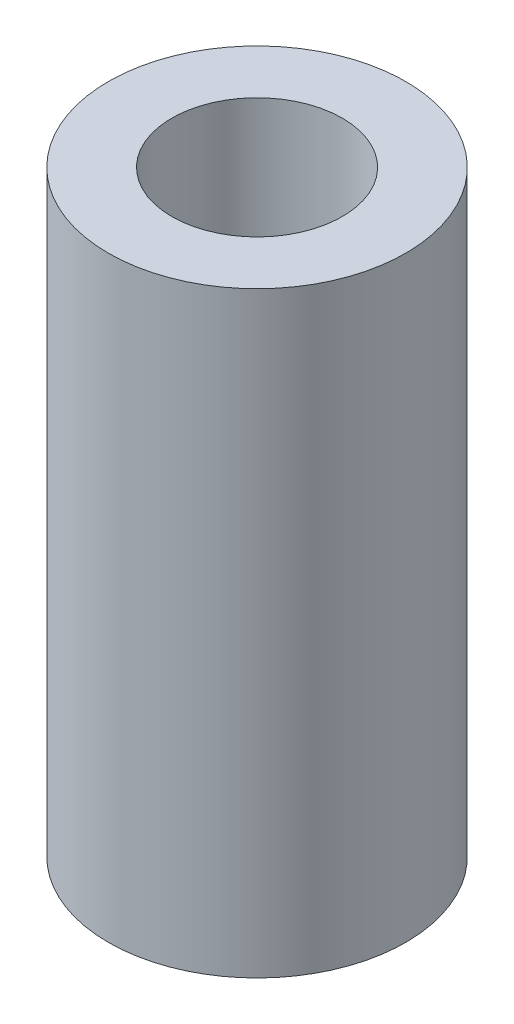
SolidWorks part; units mm, degrees
ref_plane "Front Plane" through (0, 0, 0) normal (0, 0, 1) x (1, 0, 0)
ref_plane "Top Plane" through (0, 0, 0) normal (0, 1, 0) x (1, 0, 0)
ref_plane "Right Plane" through (0, 0, 0) normal (1, 0, 0) x (0, 0, -1)
sketch "Sketch1" plane through (0, 0, 0) normal (0, 1, 0) x (1, 0, 0)
  circle A0 centre (0, 0) radius 6.975
  circle A1 centre (0, 0) radius 4
  dimension "D1" = 13.95
  dimension "D2" = 8
extrude "Boss-Extrude1" add sketch "Sketch1" along normal mid plane 28
